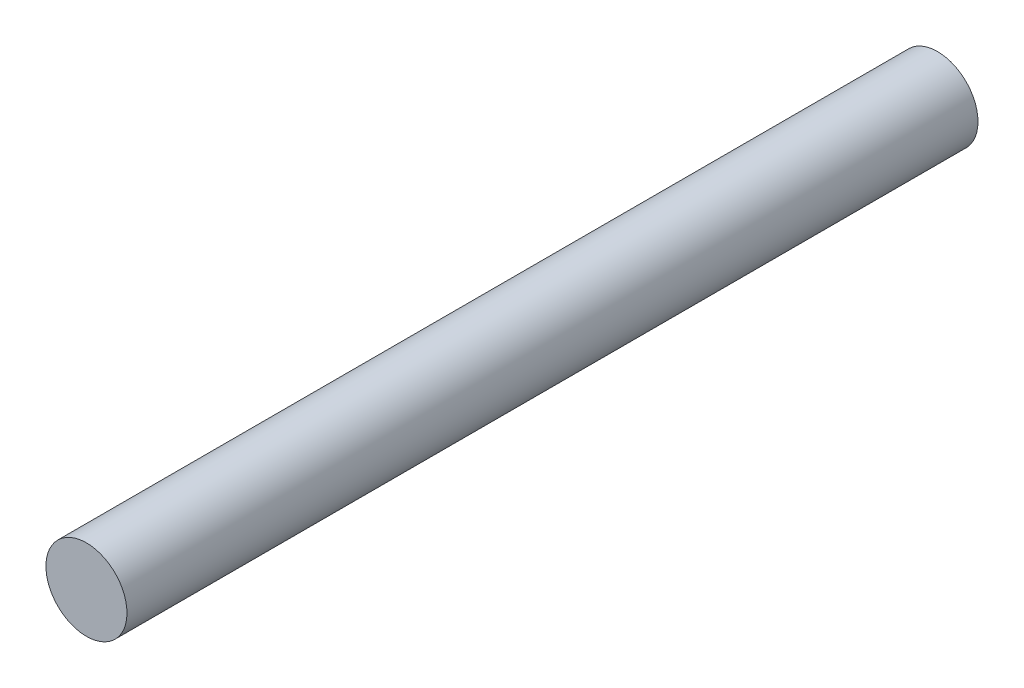
SolidWorks part; units mm, degrees
ref_plane "Front Plane" through (0, 0, 0) normal (0, 0, 1) x (1, 0, 0)
ref_plane "Top Plane" through (0, 0, 0) normal (0, 1, 0) x (1, 0, 0)
ref_plane "Right Plane" through (0, 0, 0) normal (1, 0, 0) x (0, 0, -1)
sketch "Sketch1" plane through (0, 0, 0) normal (0, 0, 1) x (1, 0, 0)
  circle A0 centre (0, 0) radius 4
  dimension "D1" = 8
extrude "Boss-Extrude1" add sketch "Sketch1" along normal blind 84
